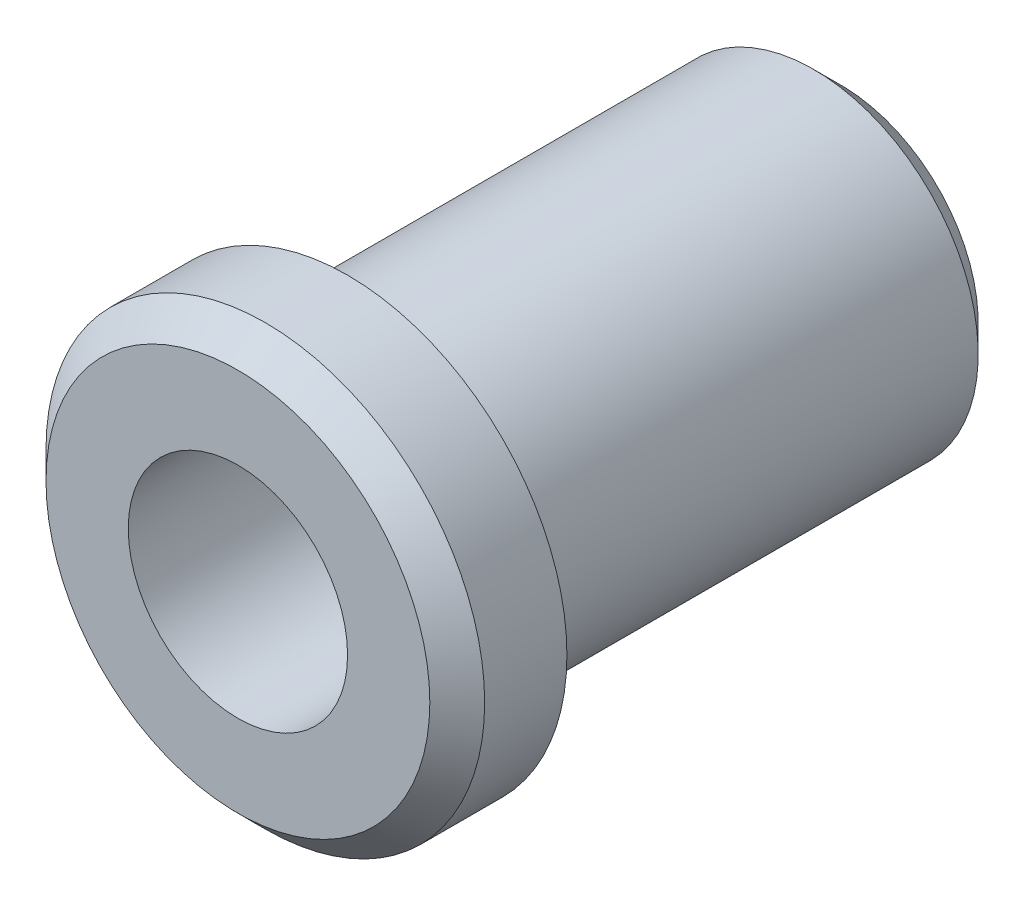
SolidWorks part; units mm, degrees
ref_plane "정면" through (0, 0, 0) normal (0, 0, 1) x (1, 0, 0)
ref_plane "윗면" through (0, 0, 0) normal (0, 1, 0) x (1, 0, 0)
ref_plane "우측면" through (0, 0, 0) normal (1, 0, 0) x (0, 0, -1)
sketch "스케치1" plane through (0, 0, 0) normal (0, 0, 1) x (1, 0, 0)
  circle A0 centre (0, 0) radius 8
  dimension "D1" = 16
extrude "보스-돌출1" add sketch "스케치1" along normal blind 4
sketch "스케치2" plane through (0, 0, 0) normal (0, 0, -1) x (-1, 0, 0)
  circle A0 centre (0, 0) radius 6
  dimension "D1" = 12
extrude "보스-돌출2" add sketch "스케치2" along normal blind 18
sketch "스케치3" plane through (0, 0, -18) normal (0, 0, -1) x (-1, 0, 0)
  circle A0 centre (0, 0) radius 4
  dimension "D1" = 8
extrude "컷-돌출1" cut sketch "스케치3" against normal through all
chamfer "모따기1" distance 1 angle 45 2 edges at (8, 0, 4) (-6, 0, -18)
